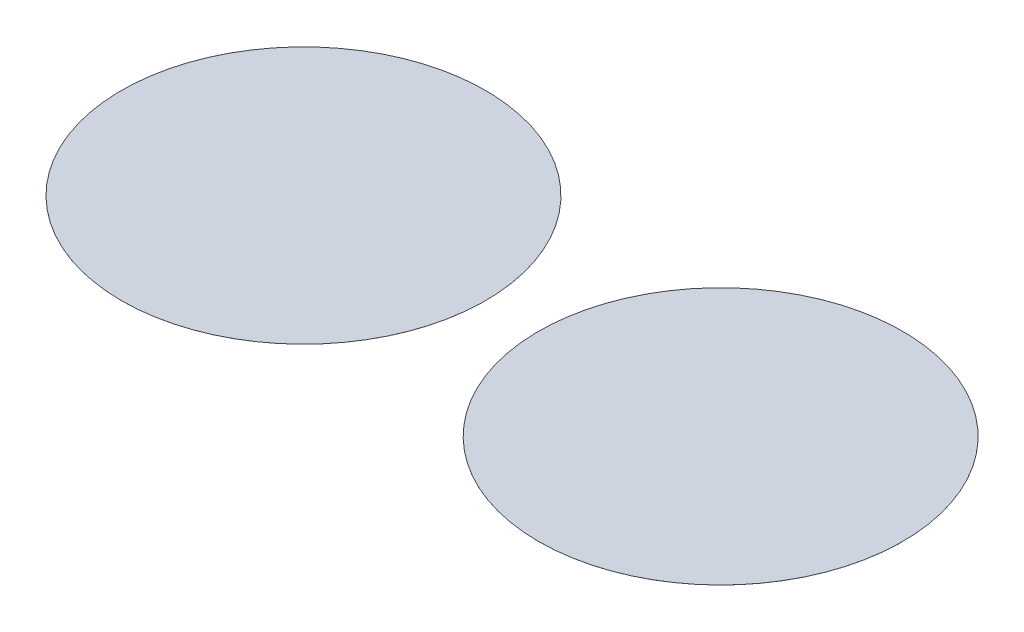
SolidWorks part; units mm, degrees
ref_plane "Front Plane" through (0, 0, 0) normal (0, 0, 1) x (1, 0, 0)
ref_plane "Top Plane" through (0, 0, 0) normal (0, 1, 0) x (1, 0, 0)
ref_plane "Right Plane" through (0, 0, 0) normal (1, 0, 0) x (0, 0, -1)
sketch "Sketch1" plane through (0, 0, 0) normal (0, 1, 0) x (1, 0, 0)
  line L0 (-5155, 0) -> (5155, 0) construction
  circle A0 centre (-5155, 0) radius 4500
  circle A1 centre (5155, 0) radius 4500
  point P3 (0, 0)
  dimension "D2" = 9000
  dimension "D1" = 10310
extrude "Boss-Extrude1" add sketch "Sketch1" along normal blind 0.5
